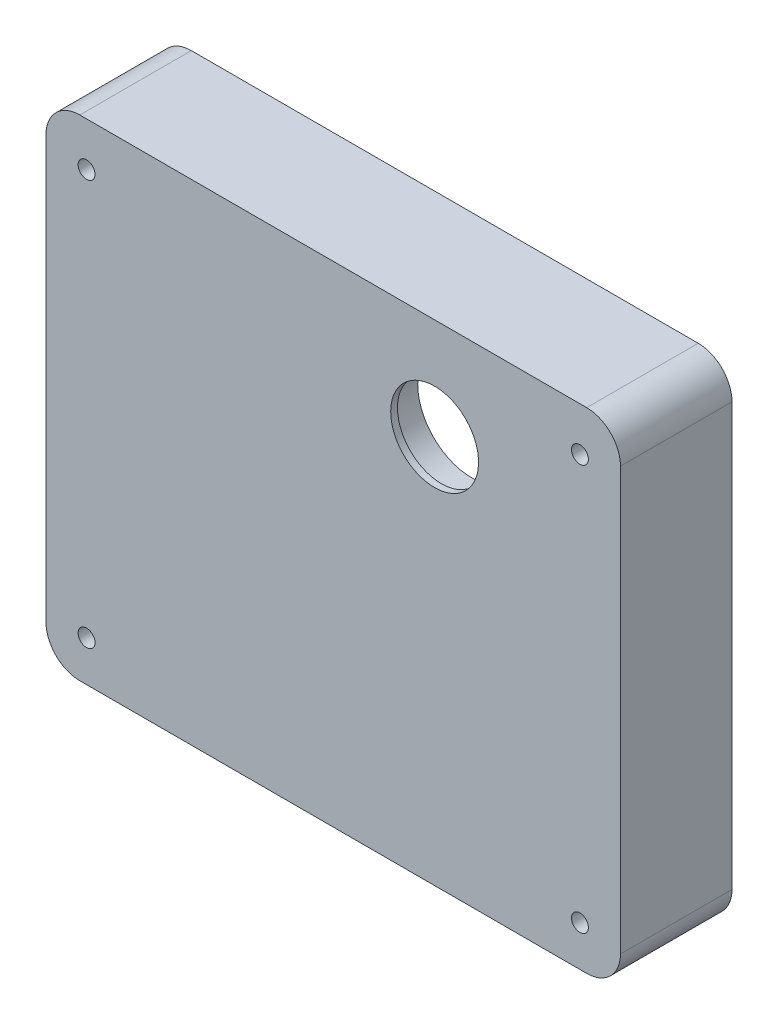
SolidWorks part; units mm, degrees
material "6063-T1"
ref_plane "Front Plane" through (0, 0, 0) normal (0, 0, 1) x (1, 0, 0)
ref_plane "Top Plane" through (0, 0, 0) normal (0, 1, 0) x (1, 0, 0)
ref_plane "Right Plane" through (0, 0, 0) normal (1, 0, 0) x (0, 0, -1)
sketch "Sketch1" plane through (0, 0, 0) normal (0, 0, 1) x (1, 0, 0)
  line L0 (55, 0) -> (-55, 0) construction
  line L1 (0, -55) -> (0, 55) construction
  line L3 (-105, 90) -> (45, 90)
  line L4 (-115, 80) -> (-115, -45)
  line L5 (-105, -55) -> (45, -55)
  line L6 (55, 80) -> (55, -45)
  circle A0 centre (0, 0) radius 50 construction
  circle A1 centre (-60, 0) radius 50 construction
  circle A2 centre (0, 60) radius 25 construction
  arc A3 (-115, -45) -> (-105, -55) centre (-105, -45) ccw
  arc A4 (45, -55) -> (55, -45) centre (45, -45) ccw
  arc A5 (45, 90) -> (55, 80) centre (45, 80) cw
  arc A6 (-105, 90) -> (-115, 80) centre (-105, 80) ccw
  dimension "D2" = 100
  dimension "D3" = 50
  dimension "D9" = 10
  dimension "D1" = 60
  dimension "D4" = 60
  dimension "D5" = 55
  dimension "D6" = 90
  dimension "D7" = 55
  dimension "D8" = 115
extrude "Boss-Extrude1" add sketch "Sketch1" along normal blind 33
sketch "Sketch2" plane through (0, 0, 0) normal (0, 0, 1) x (1, 0, 0)
  line L0 (-60, -50) -> (0, -50)
  line L1 (50, 0) -> (50, 54)
  line L2 (44, 60) -> (30.4138, 60)
  line L3 (-30.4138, 60) -> (-104, 60)
  line L4 (-110, 0) -> (-110, 54)
  arc A0 (-110, 0) -> (-60, -50) centre (-60, 0) ccw
  circle A1 centre (0, 60) radius 25 construction
  circle A2 centre (0, 0) radius 50 construction
  arc A3 (50, 54) -> (44, 60) centre (44, 54) ccw
  arc A4 (-110, 54) -> (-104, 60) centre (-104, 54) cw
  arc A5 (24.5273, 64.8387) -> (-24.5273, 64.8387) centre (0, 60) ccw
  arc A6 (0, -50) -> (50, 0) centre (0, 0) ccw
  arc A7 (24.5273, 64.8387) -> (30.4138, 60) centre (30.4138, 66) ccw
  arc A8 (-30.4138, 60) -> (-24.5273, 64.8387) centre (-30.4138, 66) ccw
  point P26 (-25, 60)
  dimension "D1" = 6
  dimension "D2" = 6
extrude "Cut-Extrude1" cut sketch "Sketch2" along normal blind 22
sketch "Sketch3" plane through (0, 0, 22) normal (0, 0, -1) x (-1, 0, 0)
  circle A0 centre (0, 0) radius 13
  circle A1 centre (60, 0) radius 13
  circle A2 centre (0, 60) radius 16 construction
  dimension "D1" = 26
  dimension "D2" = 26
  dimension "D3" = 32
extrude "Cut-Extrude2" cut sketch "Sketch3" against normal blind 8
sketch "Sketch4" plane through (0, 0, 30) normal (0, 0, -1) x (-1, 0, 0)
  circle A0 centre (0, 0) radius 10.5
  circle A1 centre (60, 0) radius 10.5
  dimension "D1" = 21
  dimension "D2" = 21
extrude "Cut-Extrude3" cut sketch "Sketch4" against normal blind 1
sketch "Sketch5" plane through (0, 0, 22) normal (0, 0, -1) x (-1, 0, 0)
  circle A0 centre (0, 60) radius 16
  circle A1 centre (0, 60) radius 16 construction
extrude "Cut-Extrude4" cut sketch "Sketch5" against normal blind 9
sketch "Sketch6" plane through (0, 0, 31) normal (0, 0, -1) x (-1, 0, 0)
  circle A0 centre (0, 60) radius 13
  dimension "D1" = 26
extrude "Cut-Extrude5" cut sketch "Sketch6" against normal through all
fillet "Fillet1" radius 2 12 edges at (48.2426, 58.2426, 22) (50, 27, 22) (35.3553, -35.3553, 22) (-30, -50, 22) (-95.3553, -35.3553, 22) (-110, 27, 22) (-108.2426, 58.2426, 22) (-67.2069, 60, 22) (-26.6038, 61.3649, 22) (0, 85, 22) (26.6038, 61.3649, 22) (37.2069, 60, 22)
fillet "Fillet2" radius 0.2 3 edges at (-13, 0, 30) (-73, 0, 30) (-16, 60, 31)
hole_wizard "M6 Tapped Hole1" positions "Sketch8" profile "Sketch7" tap size "M6" standard "ISO" end condition through all
sketch "Sketch8" plane through (0, 0, 0) normal (0, 0, -1) x (-1, 0, 0)
  line L1 (-43, 77) -> (103, 77) construction
  line L2 (-43, 77) -> (-43, -43) construction
  line L3 (-43, -43) -> (103, -43) construction
  line L4 (103, 77) -> (103, -43) construction
  line L5 (18.15, 0) -> (-18.15, 0) construction
  line L6 (0, 18.15) -> (0, -18.15) construction
  point P0 (103, 77)
  point P2 (-43, 77)
  point P4 (-43, -43)
  point P6 (103, -43)
  dimension "D1" = 120
  dimension "D2" = 43
  dimension "D3" = 43
  dimension "D4" = 146
sketch "Sketch7" plane through (-103, 77, 0) normal (1, 0, 0) x (0, 1, 0)
  line L0 (0, 0) -> (0, 33)
  line L1 (0, 33) -> (2.5, 33)
  line L2 (2.5, 33) -> (2.5, 0)
  line L5 (2.5, 0) -> (0, 0)
  line L11 (0, -6.35) -> (0, 107.95) construction
  dimension "Thru Tap Drill Dia." = 5
  dimension "Thru Tap Drill Depth" = 33
cosmetic thread "Hole Thread1" parameters "D2"=6
cosmetic thread "Hole Thread2" parameters "D2"=6
cosmetic thread "Hole Thread3" parameters "D2"=6
cosmetic thread "Hole Thread4" parameters "D2"=6
